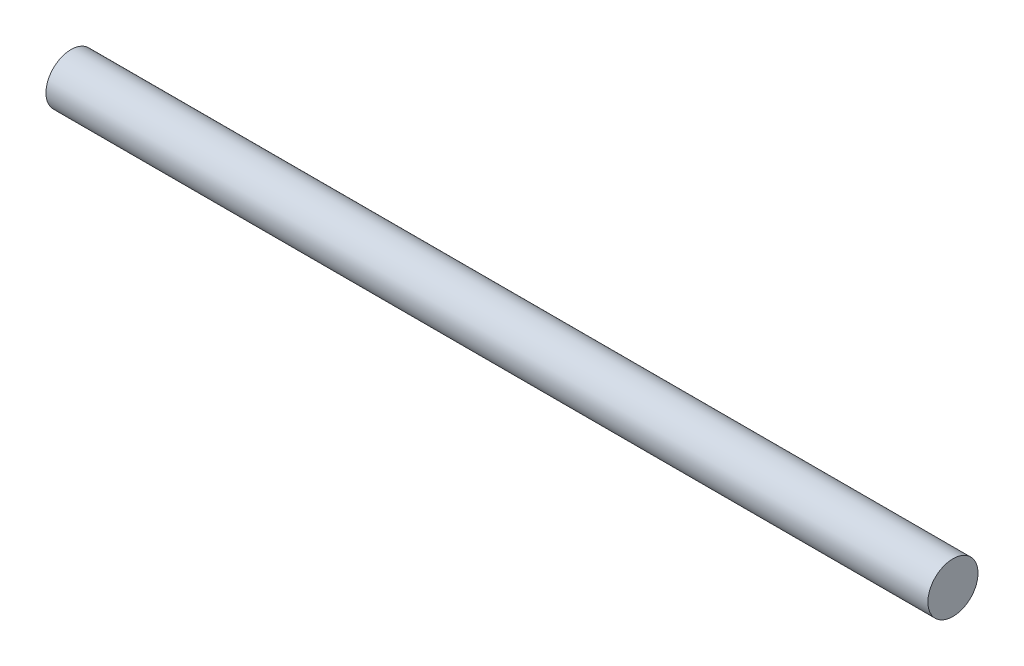
SolidWorks part; units mm, degrees
material "ABS"
ref_plane "Front Plane" through (0, 0, 0) normal (0, 0, 1) x (1, 0, 0)
ref_plane "Top Plane" through (0, 0, 0) normal (0, 1, 0) x (1, 0, 0)
ref_plane "Right Plane" through (0, 0, 0) normal (1, 0, 0) x (0, 0, -1)
sketch "Sketch2" plane through (0, 0, 0) normal (1, 0, 0) x (0, 0, -1)
  circle A0 centre (0, 0) radius 5
  dimension "D1" = 10
extrude "Boss-Extrude1" add sketch "Sketch2" along normal mid plane 176
